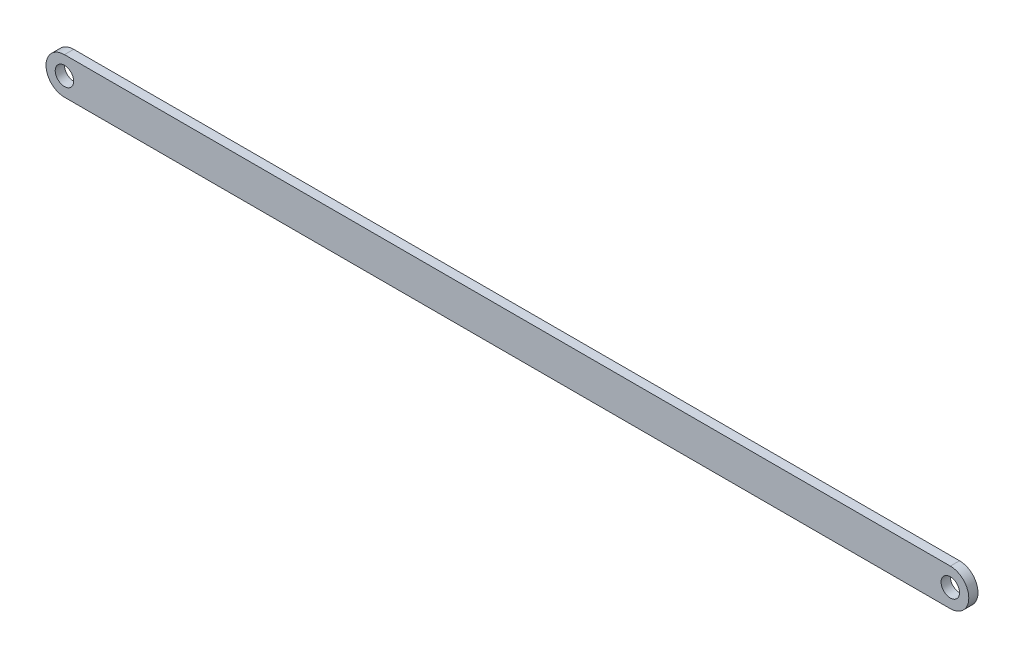
SolidWorks part; units mm, degrees
ref_plane "Front Plane" through (0, 0, 0) normal (0, 0, 1) x (1, 0, 0)
ref_plane "Top Plane" through (0, 0, 0) normal (0, 1, 0) x (1, 0, 0)
ref_plane "Right Plane" through (0, 0, 0) normal (1, 0, 0) x (0, 0, -1)
sketch "Sketch1" plane through (0, 0, 0) normal (0, 0, 1) x (1, 0, 0)
  line L0 (-152.4, 0) -> (152.4, 0) construction
  line L1 (-152.4, 6.35) -> (152.4, 6.35)
  line L2 (-152.4, -6.35) -> (152.4, -6.35)
  arc A0 (-152.4, 6.35) -> (-152.4, -6.35) centre (-152.4, 0) ccw
  arc A1 (152.4, -6.35) -> (152.4, 6.35) centre (152.4, 0) ccw
  circle A2 centre (-152.4, 0) radius 3.175
  circle A3 centre (152.4, 0) radius 3.175
  point P2 (0, 0)
  dimension "D3" = 6.35
  dimension "D1" = 12.7
  dimension "D2" = 304.8
extrude "Boss-Extrude2" add sketch "Sketch1" along normal blind 3.175 contours L2 A1 L1 A0 | A2 | A3
